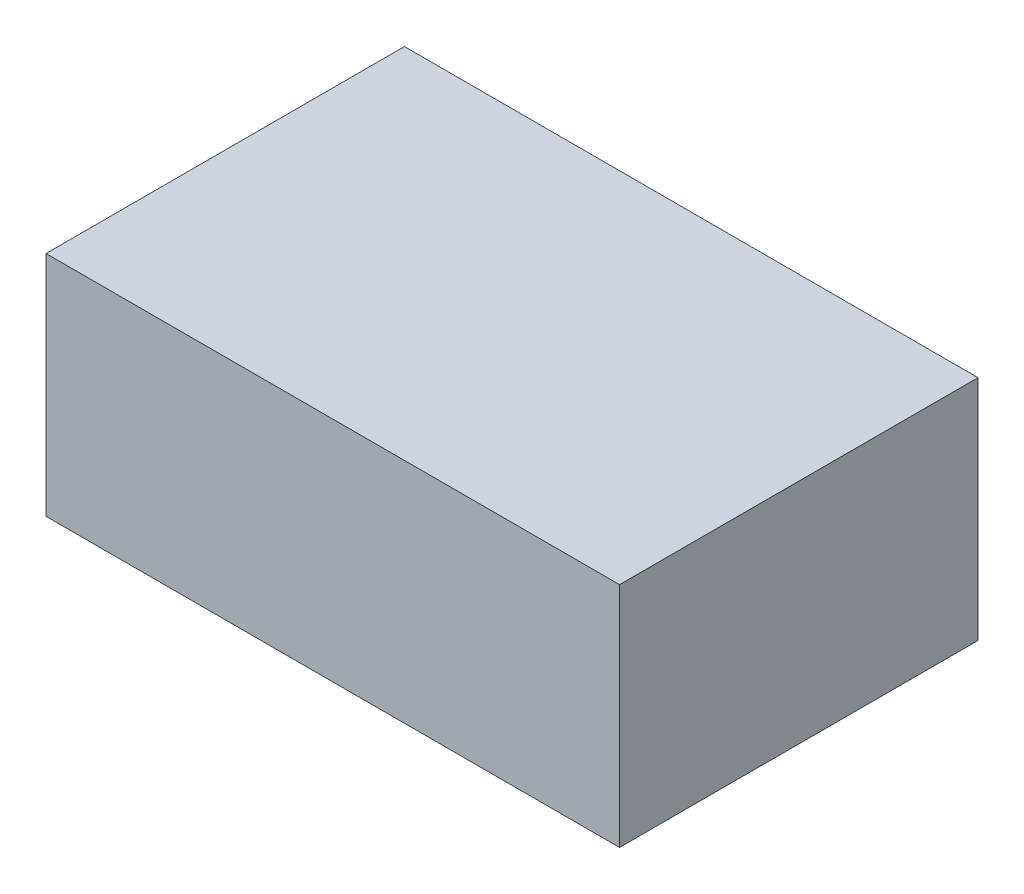
SolidWorks part; units mm, degrees
ref_plane "Front Plane" through (0, 0, 0) normal (0, 0, 1) x (1, 0, 0)
ref_plane "Top Plane" through (0, 0, 0) normal (0, 1, 0) x (1, 0, 0)
ref_plane "Right Plane" through (0, 0, 0) normal (1, 0, 0) x (0, 0, -1)
sketch "Sketch1" plane through (0, 0, 0) normal (0, 1, 0) x (1, 0, 0)
  line L1 (-4, 2.5) -> (4, 2.5)
  line L2 (-4, 2.5) -> (-4, -2.5)
  line L3 (-4, -2.5) -> (4, -2.5)
  line L4 (4, 2.5) -> (4, -2.5)
  point P4 (0, 2.5)
  point P6 (-4, 0)
  dimension "D1" = 8
  dimension "D2" = 5
extrude "Boss-Extrude1" add sketch "Sketch1" along normal blind 3.175
